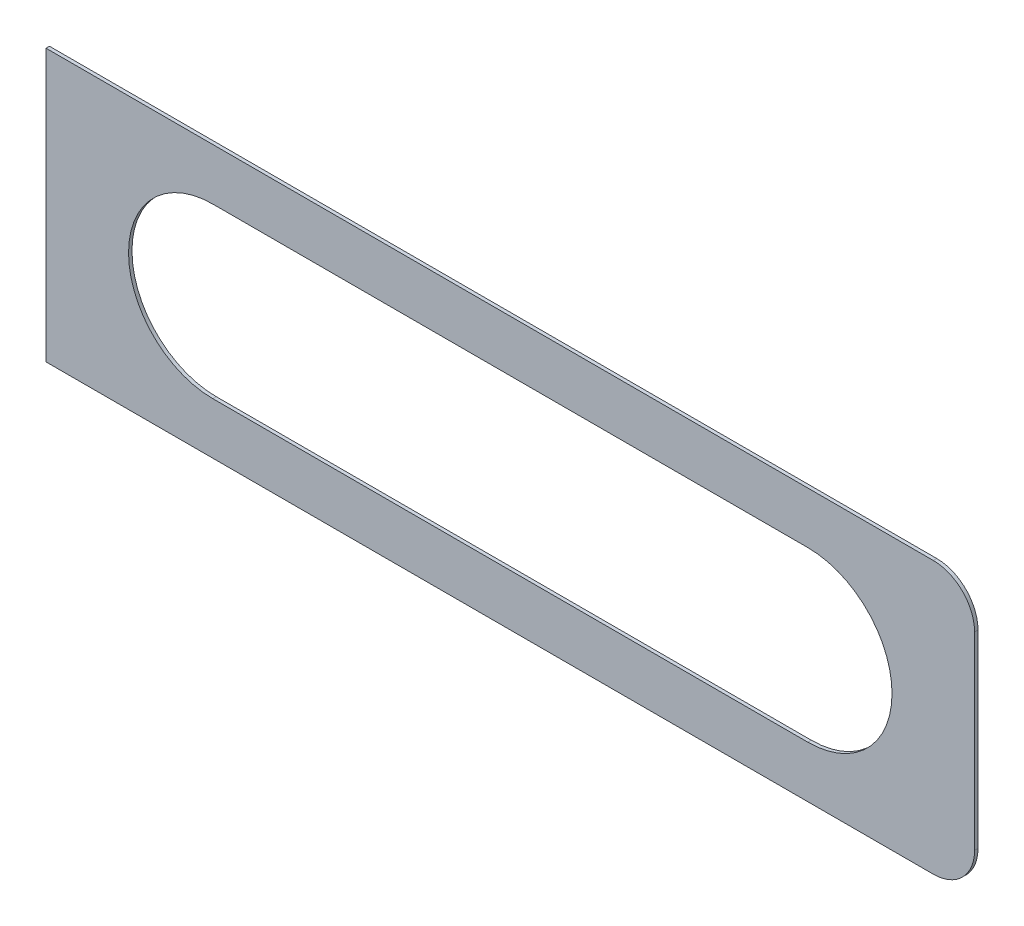
SolidWorks part; units mm, degrees
ref_plane "Front Plane" through (0, 0, 0) normal (0, 0, 1) x (1, 0, 0)
ref_plane "Top Plane" through (0, 0, 0) normal (0, 1, 0) x (1, 0, 0)
ref_plane "Right Plane" through (0, 0, 0) normal (1, 0, 0) x (0, 0, -1)
sketch "Sketch1" plane through (0, 0, 0) normal (0, 0, 1) x (1, 0, 0)
  line L1 (-34.29, 10.033) -> (31.242, 10.033)
  line L2 (-34.29, 10.033) -> (-34.29, -10.033)
  line L3 (-34.29, -10.033) -> (31.242, -10.033)
  line L4 (34.29, 6.985) -> (34.29, -6.985)
  line L5 (-34.29, 10.033) -> (34.29, -10.033) construction
  line L6 (-34.29, -10.033) -> (34.29, 10.033) construction
  arc A0 (31.242, -10.033) -> (34.29, -6.985) centre (31.242, -6.985) ccw
  arc A1 (34.29, 6.985) -> (31.242, 10.033) centre (31.242, 6.985) ccw
  point P0 (0, 0)
  dimension "D3" = 3.048
  dimension "D1" = 20.066
  dimension "D2" = 68.58
extrude "Boss-Extrude1" add sketch "Sketch1" along normal blind 0.254
sketch "Sketch2" plane through (0, 0, 0.254) normal (0, 0, 1) x (1, 0, 0)
  line L0 (-21.971, 0) -> (21.971, 0) construction
  line L1 (-21.971, 6.223) -> (21.971, 6.223)
  line L2 (-21.971, -6.223) -> (21.971, -6.223)
  line L3 (34.29, -6.985) -> (34.29, 6.985) construction
  arc A0 (-21.971, 6.223) -> (-21.971, -6.223) centre (-21.971, 0) ccw
  arc A1 (21.971, -6.223) -> (21.971, 6.223) centre (21.971, 0) ccw
  point P3 (0, 0)
  dimension "D3" = 56.388
  dimension "D1" = 12.446
  dimension "D2" = 6.096
extrude "Cut-Extrude1" cut sketch "Sketch2" against normal blind 0.254
